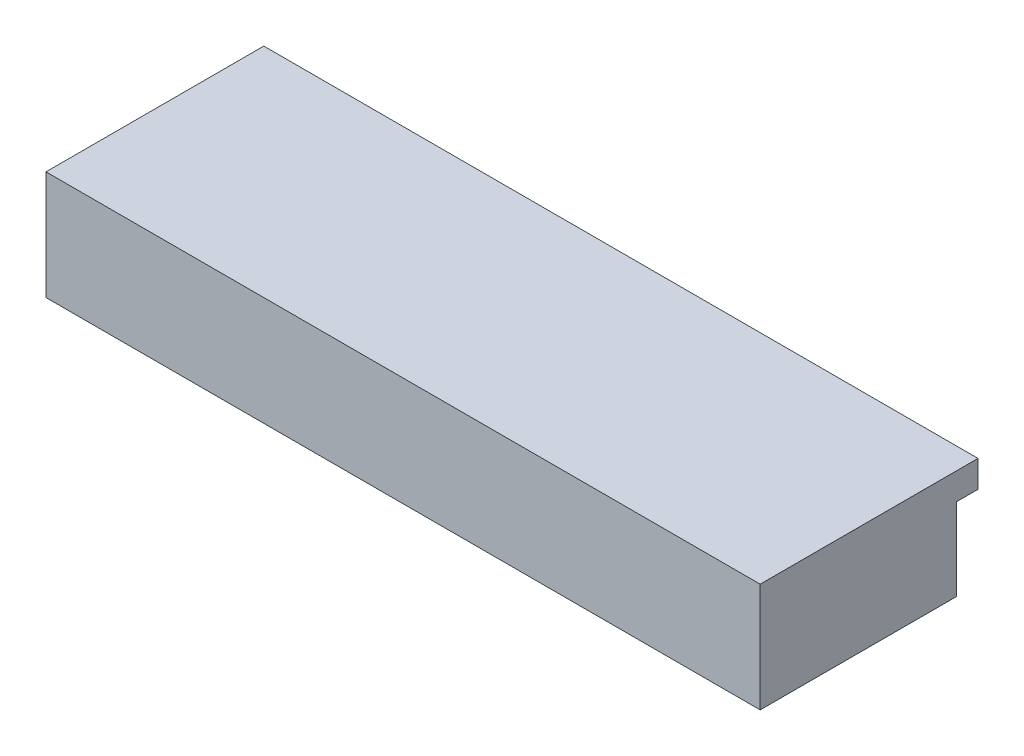
SolidWorks part; units mm, degrees
ref_plane "Plan de face" through (0, 0, 0) normal (0, 0, 1) x (1, 0, 0)
ref_plane "Plan de dessus" through (0, 0, 0) normal (0, 1, 0) x (1, 0, 0)
ref_plane "Plan de droite" through (0, 0, 0) normal (1, 0, 0) x (0, 0, -1)
sketch "Esquisse3" plane through (0, 0, 0) normal (0, 0, 1) x (1, 0, 0)
  line L4 (238, 25) -> (-162, 25)
  line L5 (-162, 25) -> (-162, -15)
  line L6 (-162, -15) -> (238, -15)
  line L7 (238, -15) -> (238, 25)
  line L8 (238, 25) -> (-162, 25)
  line L9 (-162, 25) -> (-162, -15)
  line L10 (-162, -15) -> (238, -15)
  line L11 (238, -15) -> (238, 25)
  dimension "D1" = 0
extrude "Extrusion1" add sketch "Esquisse3" along normal blind 110
sketch "Esquisse8" plane through (0, 25, 0) normal (0, 1, 0) x (1, 0, 0)
  line L0 (-162, -110) -> (-162, 0) construction
  line L1 (238, -110) -> (-162, -110)
  line L2 (238, -110) -> (238, 12)
  line L3 (238, 12) -> (-162, 12)
  line L4 (-162, -110) -> (-162, 12)
  line L5 (238, 0) -> (-162, 0) construction
  dimension "D1" = 12
extrude "Extrusion3" add sketch "Esquisse8" along normal blind 15
sketch "Esquisse9" plane through (0, 0, 0) normal (0, 0, -1) x (-1, 0, 0)
  line L0 (-35.5, 10.75) -> (-57.5, 10.75) construction
  line L1 (-57.5, 9.75) -> (-57.5, 0.25) construction
  line L2 (-57.5, -0.75) -> (-35.5, -0.75) construction
  line L3 (-35.5, 0.25) -> (-35.5, 9.75) construction
  line L4 (-118, -6) -> (112, -6)
  line L5 (112, -6) -> (112, 16)
  line L6 (112, 16) -> (-118, 16)
  line L7 (-118, 16) -> (-118, -6)
  line L8 (-118, -6) -> (112, -6)
  line L9 (112, -6) -> (112, 16)
  line L10 (112, 16) -> (-118, 16)
  line L11 (-118, 16) -> (-118, -6)
  line L12 (49.5, 2.5) -> (49.5, 9.5) construction
  line L13 (16, 1.5) -> (49.5, 1.5) construction
  line L14 (16, 9.5) -> (16, 2.5) construction
  line L15 (49.5, 10.5) -> (16, 10.5) construction
  line L16 (-35.5, 10.75) -> (-57.5, 10.75)
  line L17 (-57.5, 9.75) -> (-57.5, 0.25)
  line L18 (-57.5, -0.75) -> (-35.5, -0.75)
  line L19 (-35.5, 0.25) -> (-35.5, 9.75)
  line L20 (49.5, 2.5) -> (49.5, 9.5)
  line L21 (16, 1.5) -> (49.5, 1.5)
  line L22 (16, 9.5) -> (16, 2.5)
  line L23 (49.5, 10.5) -> (16, 10.5)
  dimension "D1" = 0
sketch "Esquisse11" plane through (0, -15, 0) normal (0, -1, 0) x (1, 0, 0)
  line L4 (-162, 0) -> (238, 0)
  line L5 (238, 0) -> (238, 110)
  line L6 (238, 110) -> (-162, 110)
  line L7 (-162, 110) -> (-162, 0)
  line L8 (-162, 0) -> (238, 0)
  line L9 (238, 0) -> (238, 110)
  line L10 (238, 110) -> (-162, 110)
  line L11 (-162, 110) -> (-162, 0)
  dimension "D1" = 0
extrude "Extrusion5" add sketch "Esquisse11" along normal blind 6
sketch "Esquisse10" plane through (0, 0, 0) normal (0, 0, -1) x (-1, 0, 0)
  line L0 (-35.5, 0.25) -> (-35.5, 9.75) construction
  line L1 (-31.5, -3) -> (-61.5, -3)
  line L2 (-30.5, -2) -> (-30.5, 12)
  line L3 (-31.5, 13) -> (-61.5, 13)
  line L4 (-62.5, -2) -> (-62.5, 12)
  line L5 (-57.5, -0.75) -> (-35.5, -0.75) construction
  line L6 (16, 1.5) -> (49.5, 1.5) construction
  line L7 (51.75, 0) -> (12.75, 0)
  line L8 (52.75, 1) -> (52.75, 11)
  line L9 (51.75, 12) -> (12.75, 12)
  line L10 (11.75, 1) -> (11.75, 11)
  line L12 (16, 9.5) -> (16, 2.5) construction
  line L14 (59.5, -8) -> (59.5, -19)
  line L15 (70.25, -6) -> (61.5, -6)
  line L16 (-83, 19) -> (70.25, 19)
  line L18 (57.5, -21) -> (-68.5, -21)
  line L19 (-70.5, -19) -> (-70.5, -8)
  line L20 (-72.5, -6) -> (-83, -6)
  arc A0 (70.25, -6) -> (70.25, 19) centre (70.25, 6.5) ccw
  arc A1 (-83, 19) -> (-83, -6) centre (-83, 6.5) ccw
  arc A2 (59.5, -8) -> (61.5, -6) centre (61.5, -8) cw
  arc A3 (59.5, -19) -> (57.5, -21) centre (57.5, -19) cw
  arc A4 (-68.5, -21) -> (-70.5, -19) centre (-68.5, -19) cw
  arc A5 (-72.5, -6) -> (-70.5, -8) centre (-72.5, -8) cw
  arc A6 (51.75, 0) -> (52.75, 1) centre (51.75, 1) ccw
  arc A7 (51.75, 12) -> (52.75, 11) centre (51.75, 11) cw
  arc A8 (12.75, 12) -> (11.75, 11) centre (12.75, 11) ccw
  arc A9 (12.75, 0) -> (11.75, 1) centre (12.75, 1) cw
  arc A10 (-31.5, -3) -> (-30.5, -2) centre (-31.5, -2) ccw
  arc A11 (-30.5, 12) -> (-31.5, 13) centre (-31.5, 12) ccw
  arc A12 (-61.5, 13) -> (-62.5, 12) centre (-61.5, 12) ccw
  arc A13 (-61.5, -3) -> (-62.5, -2) centre (-61.5, -2) cw
  circle A14 centre (-86.5, 6.5) radius 3
  circle A15 centre (-20.5, 6.5) radius 3
  circle A16 centre (72.75, 6.5) radius 3
  point P30 (59.5, -21)
  point P33 (-70.5, -21)
  point P38 (52.75, 0)
  point P43 (11.75, 12)
  point P46 (11.75, 0)
  point P49 (-30.5, -3)
  point P54 (-62.5, 13)
  point P57 (-62.5, -3)
  dimension "D9" = 25
  dimension "D10" = 12.5
  dimension "D16" = 2
  dimension "D17" = 1
  dimension "D18" = 6
  dimension "D20" = 6
  dimension "D21" = 6
  dimension "D1" = 32
  dimension "D2" = 16
  dimension "D3" = 5
  dimension "D4" = 2.25
  dimension "D5" = 12
  dimension "D6" = 41
  dimension "D7" = 1.5
  dimension "D8" = 4.25
  dimension "D11" = 17.5
  dimension "D12" = 7
  dimension "D13" = 130
  dimension "D14" = 8
  dimension "D15" = 40
  dimension "D19" = 24
  dimension "D22" = 10
  dimension "D23" = 20
extrude "Extrusion4" cut sketch "Esquisse10" against normal blind 1.5
sketch "Esquisse12" plane through (0, 0, 0) normal (0, 0, -1) x (-1, 0, 0)
  line L4 (-30.5, -2) -> (-30.5, 12)
  line L5 (-31.5, 13) -> (-61.5, 13)
  line L6 (-62.5, 12) -> (-62.5, -2)
  line L7 (-61.5, -3) -> (-31.5, -3)
  line L8 (-30.5, -2) -> (-30.5, 12)
  line L9 (-31.5, 13) -> (-61.5, 13)
  line L10 (-62.5, 12) -> (-62.5, -2)
  line L11 (-61.5, -3) -> (-31.5, -3)
  line L14 (52.75, 1) -> (52.75, 11)
  line L15 (51.75, 12) -> (12.75, 12)
  line L16 (11.75, 11) -> (11.75, 1)
  line L17 (12.75, 0) -> (51.75, 0)
  line L18 (52.75, 1) -> (52.75, 11)
  line L19 (51.75, 12) -> (12.75, 12)
  line L20 (11.75, 11) -> (11.75, 1)
  line L21 (12.75, 0) -> (51.75, 0)
  circle A1 centre (-86.5, 6.5) radius 3
  circle A2 centre (-86.5, 6.5) radius 3
  circle A3 centre (-20.5, 6.5) radius 3
  arc A4 (-31.5, -3) -> (-30.5, -2) centre (-31.5, -2) ccw
  arc A5 (-30.5, 12) -> (-31.5, 13) centre (-31.5, 12) ccw
  arc A6 (-61.5, 13) -> (-62.5, 12) centre (-61.5, 12) ccw
  arc A7 (-62.5, -2) -> (-61.5, -3) centre (-61.5, -2) ccw
  arc A8 (-31.5, -3) -> (-30.5, -2) centre (-31.5, -2) ccw
  arc A9 (-30.5, 12) -> (-31.5, 13) centre (-31.5, 12) ccw
  arc A10 (-61.5, 13) -> (-62.5, 12) centre (-61.5, 12) ccw
  arc A11 (-62.5, -2) -> (-61.5, -3) centre (-61.5, -2) ccw
  circle A12 centre (-20.5, 6.5) radius 3
  circle A13 centre (72.75, 6.5) radius 3
  circle A14 centre (72.75, 6.5) radius 3
  arc A18 (51.75, 0) -> (52.75, 1) centre (51.75, 1) ccw
  arc A19 (52.75, 11) -> (51.75, 12) centre (51.75, 11) ccw
  arc A20 (12.75, 12) -> (11.75, 11) centre (12.75, 11) ccw
  arc A21 (11.75, 1) -> (12.75, 0) centre (12.75, 1) ccw
  arc A22 (51.75, 0) -> (52.75, 1) centre (51.75, 1) ccw
  arc A23 (52.75, 11) -> (51.75, 12) centre (51.75, 11) ccw
  arc A24 (12.75, 12) -> (11.75, 11) centre (12.75, 11) ccw
  arc A25 (11.75, 1) -> (12.75, 0) centre (12.75, 1) ccw
  dimension "D1" = 0
  dimension "D2" = 0
  dimension "D3" = 0
  dimension "D4" = 0
  dimension "D5" = 0
extrude "Extrusion6" cut sketch "Esquisse12" against normal blind 20
